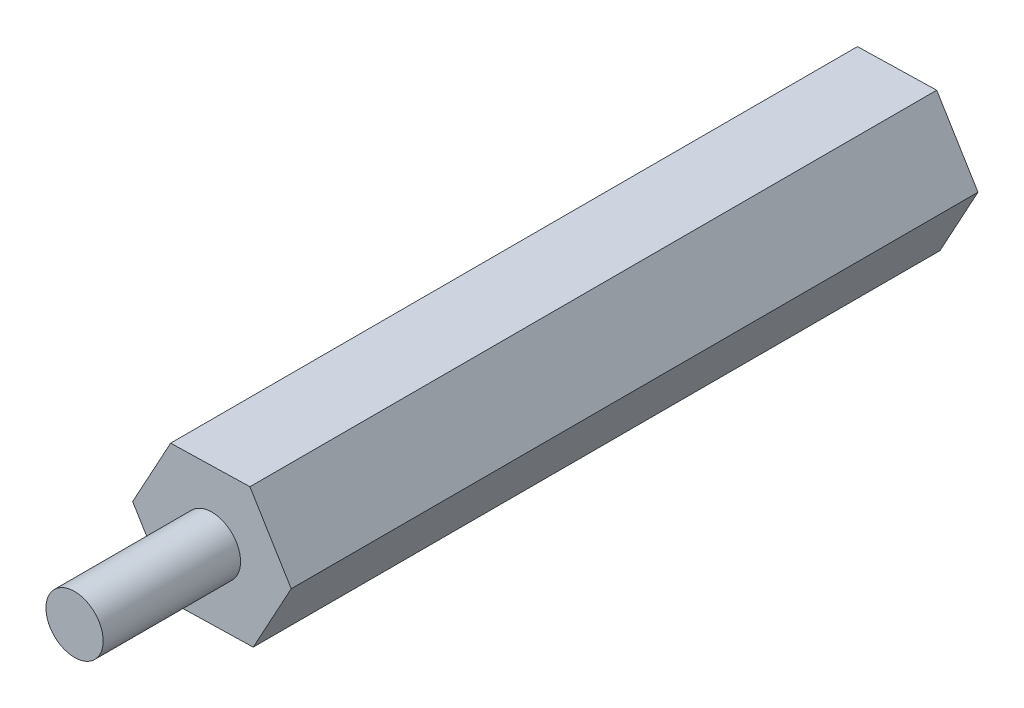
SolidWorks part; units mm, degrees
ref_plane "前视基准面" through (0, 0, 0) normal (0, 0, 1) x (1, 0, 0)
ref_plane "上视基准面" through (0, 0, 0) normal (0, 1, 0) x (1, 0, 0)
ref_plane "右视基准面" through (0, 0, 0) normal (1, 0, 0) x (0, 0, -1)
sketch "草图1" plane through (0, 0, 0) normal (0, 0, 1) x (1, 0, 0)
  line L1 (1.66, 3.0405) -> (-1.8031, 2.9578)
  line L2 (-1.8031, 2.9578) -> (-3.4631, -0.0827)
  line L3 (-3.4631, -0.0827) -> (-1.66, -3.0405)
  line L4 (-1.66, -3.0405) -> (1.8031, -2.9578)
  line L5 (1.8031, -2.9578) -> (3.4631, 0.0827)
  line L6 (3.4631, 0.0827) -> (1.66, 3.0405)
  circle A0 centre (0, 0) radius 3 construction
  dimension "D1" = 6
extrude "凸台-拉伸1" add sketch "草图1" along normal blind 30
sketch "草图2" plane through (0, 0, 30) normal (0, 0, 1) x (1, 0, 0)
  circle A0 centre (0, 0) radius 1.25
  dimension "D1" = 2.5
extrude "凸台-拉伸2" add sketch "草图2" along normal blind 6
sketch "草图3" plane through (0, 0, 0) normal (0, 0, -1) x (-1, 0, 0)
  circle A0 centre (0, 0) radius 1.25
  dimension "D1" = 2.5
extrude "切除-拉伸1" cut sketch "草图3" against normal blind 20
